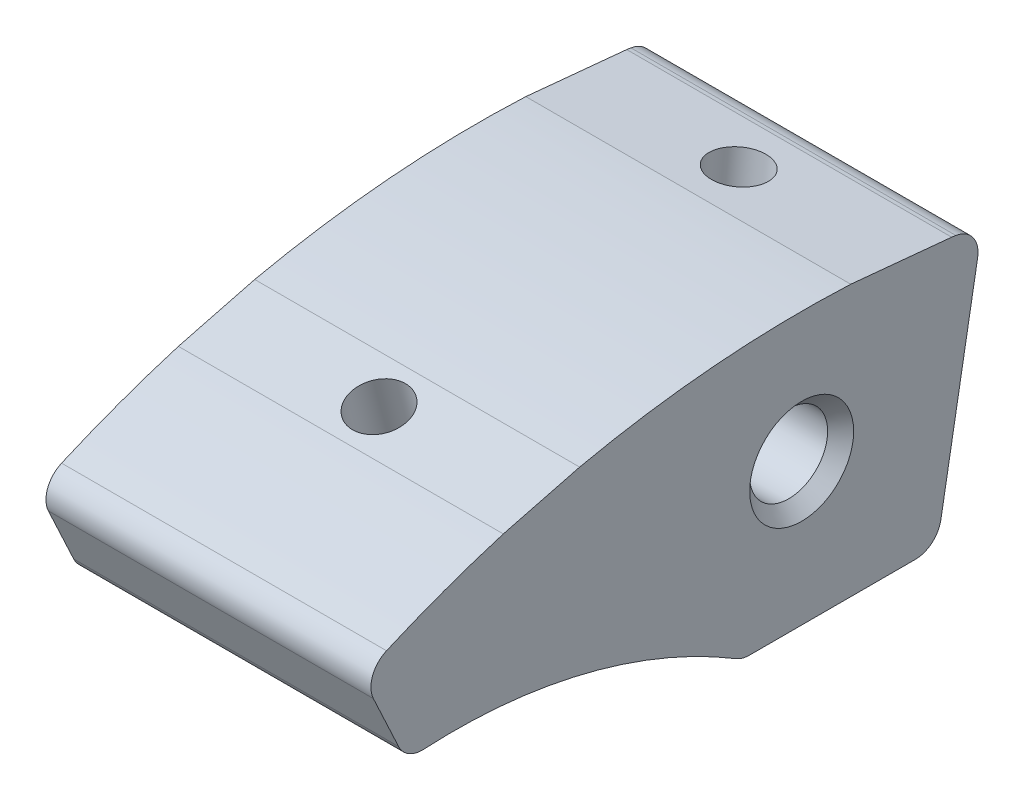
SolidWorks part; units mm, degrees
material "7075-T6 (SN)"
ref_plane "Front Plane" through (0, 0, 0) normal (0, 0, 1) x (1, 0, 0)
ref_plane "Top Plane" through (0, 0, 0) normal (0, 1, 0) x (1, 0, 0)
ref_plane "Right Plane" through (0, 0, 0) normal (1, 0, 0) x (0, 0, -1)
sketch "Sketch1" plane through (0, 0, 0) normal (1, 0, 0) x (0, 0, -1)
  line L0 (0, 0) -> (0, 80) construction
  line L1 (0, 0) -> (-33.8095, 72.5046) construction
  line L2 (13.8919, 78.7846) -> (0, 0) construction
  line L3 (-33.8095, 72.5046) -> (-30.4285, 65.2542)
  line L4 (-27.2299, 72.0245) -> (-25.5394, 68.3993)
  line L5 (-4.5811, 59.0885) -> (10.4189, 59.0885)
  line L6 (10.4189, 59.0885) -> (13.8919, 78.7846)
  line L7 (0, 0) -> (-8.3623, 79.5618) construction
  line L8 (-6.6951, 63.6998) -> (-8.0487, 76.5782)
  circle A0 centre (0, 0) radius 80 construction
  circle A1 centre (0, 70) radius 3
  arc A2 (-33.8095, 72.5046) -> (13.8919, 78.7846) centre (0, 0) cw
  arc A3 (-30.4285, 65.2542) -> (-4.5811, 59.0885) centre (-26.7497, 23.4156) cw
  arc A4 (-27.2299, 72.0245) -> (13.3709, 75.8302) centre (0, 0) cw
  arc A5 (-25.5394, 68.3993) -> (-2.9976, 61.6365) centre (-26.7497, 23.4156) cw
  dimension "D1" = 160
  dimension "D2" = 6
  dimension "D7" = 42
  dimension "D10" = 3
  dimension "D12" = 3
  dimension "D3" = 10
  dimension "D4" = 25
  dimension "D5" = 10
  dimension "D6" = 20
  dimension "D8" = 15
  dimension "D9" = 8
  dimension "D11" = 6
  dimension "D13" = 4
extrude "Boss-Extrude1" add sketch "Sketch1" along normal blind 25
fillet "Fillet2" radius 2 5 edges at (12.5, 78.7846, -13.8919) (12.5, 59.0885, -10.4189) (12.5, 59.0885, 4.5811) (12.5, 65.2542, 30.4285) (12.5, 72.5046, 33.8095)
sketch "Sketch3" plane through (25, 0, 0) normal (1, 0, 0) x (0, 0, -1)
  line L0 (0, 0) -> (-20.0304, 77.4518) construction
  line L1 (-23.9534, 80.5095) -> (-18.0817, 82.028)
  line L2 (-23.9534, 80.5095) -> (-22.9519, 76.6369)
  line L3 (-22.9519, 76.6369) -> (-17.0801, 78.1554)
  line L4 (-18.0817, 82.028) -> (-17.0801, 78.1554)
  line L5 (3.777, 89.9108) -> (11.5401, 89.1633)
  line L6 (3.777, 89.9108) -> (3.777, 79.9108)
  line L7 (3.777, 79.9108) -> (11.5401, 79.1633)
  line L8 (11.5401, 89.1633) -> (11.5401, 79.1633)
  line L9 (0, 0) -> (7.6677, 79.6317) construction
  line L10 (0, 0) -> (0, 80) construction
  arc A0 (11.8672, 79.1149) -> (-31.9393, 73.3477) centre (0, 0) ccw construction
  circle A1 centre (0, 0) radius 80 construction
  dimension "D5" = 160
  dimension "D1" = 10
  dimension "D2" = 4
  dimension "D3" = 2
  dimension "D4" = 9
  dimension "D6" = 5.5
  dimension "D7" = 14.5
extrude "Cut-Extrude1" cut sketch "Sketch3" against normal through all
hole_wizard "M5 Tapped Hole1" positions "Sketch7" profile "Sketch8" tap size "M5" standard "ISO"
sketch "Sketch7" plane through (0, 77.3961, 20.016) normal (0, 0.9681, 0.2504) x (1, 0, 0)
  line L4 (12.5, -3.0325) -> (12.5, 3.0325) construction
  line L5 (0, -3.0325) -> (25, -3.0325) construction
  line L6 (0, 3.0325) -> (25, 3.0325) construction
  point P0 (12.5, 0)
sketch "Sketch8" plane through (12.5, 77.3961, 20.016) normal (1, 0, 0) x (0, -0.2504, 0.9681)
  line L0 (0, 0) -> (0, 23.6618)
  line L1 (0, 23.6618) -> (2.1, 22.4)
  line L2 (2.1, 22.4) -> (2.1, 0)
  line L5 (2.1, 0) -> (0, 0)
  line L10 (0, 23.6618) -> (-2.1, 22.4) construction
  line L11 (0, -6.35) -> (0, 107.95) construction
  dimension "Tap Drill Dia." = 4.2
  dimension "Tap Drill Depth" = 22.4
  dimension "Drill Angle" = 118
hole_wizard "M5 Tapped Hole2" positions "Sketch10" profile "Sketch9" tap size "M5" standard "ISO"
sketch "Sketch10" plane through (0, 79.537, -7.6585) normal (0, 0.9954, -0.0958) x (1, 0, 0)
  line L3 (12.5, -3.8995) -> (12.5, 3.8995) construction
  line L4 (0, -3.8995) -> (25, -3.8995) construction
  line L5 (0, 3.8995) -> (25, 3.8995) construction
  point P0 (12.5, 0)
sketch "Sketch9" plane through (12.5, 79.537, -7.6585) normal (1, 0, 0) x (0, 0.0958, 0.9954)
  line L0 (0, 0) -> (0, 23.6618)
  line L1 (0, 23.6618) -> (2.1, 22.4)
  line L2 (2.1, 22.4) -> (2.1, 0)
  line L5 (2.1, 0) -> (0, 0)
  line L10 (0, 23.6618) -> (-2.1, 22.4) construction
  line L11 (0, -6.35) -> (0, 107.95) construction
  dimension "Tap Drill Dia." = 4.2
  dimension "Tap Drill Depth" = 22.4
  dimension "Drill Angle" = 118
sketch "Sketch11" plane through (0, 59.0885, 0) normal (0, -1, 0) x (-1, 0, 0)
  line L0 (0, 0) -> (-25, 0) construction
  line L1 (-25, -4.0175) -> (-25, 8.7407) construction
hole_wizard "M4 Tapped Hole1" positions "Sketch13" profile "Sketch12" tap size "M4" standard "ISO"
sketch "Sketch13" plane through (0, 59.0885, 0) normal (0, -1, 0) x (-1, 0, 0)
  line L0 (0, 0) -> (-25, 0) construction
  line L1 (-12.5, -4.0175) -> (-12.5, 10.7103) construction
  line L2 (-25, -4.0175) -> (0, -4.0175) construction
  line L3 (-25, 10.7103) -> (0, 10.7103) construction
  point P0 (-6.5, 0)
  point P4 (-18.5, 0)
  dimension "D1" = 12
  dimension "D2" = 6
sketch "Sketch12" plane through (6.5, 59.0885, 0) normal (1, 0, 0) x (0, 0, -1)
  line L0 (0, 0) -> (0, 11.0914)
  line L1 (0, 11.0914) -> (1.65, 10.1)
  line L2 (1.65, 10.1) -> (1.65, 0)
  line L5 (1.65, 0) -> (0, 0)
  line L10 (0, 11.0914) -> (-1.65, 10.1) construction
  line L11 (0, -6.35) -> (0, 107.95) construction
  dimension "Tap Drill Dia." = 3.3
  dimension "Tap Drill Depth" = 10.1
  dimension "Drill Angle" = 118
chamfer "Chamfer1" distance 1 angle 45 2 edges at (25, 70, -3) (0, 70, -3)
